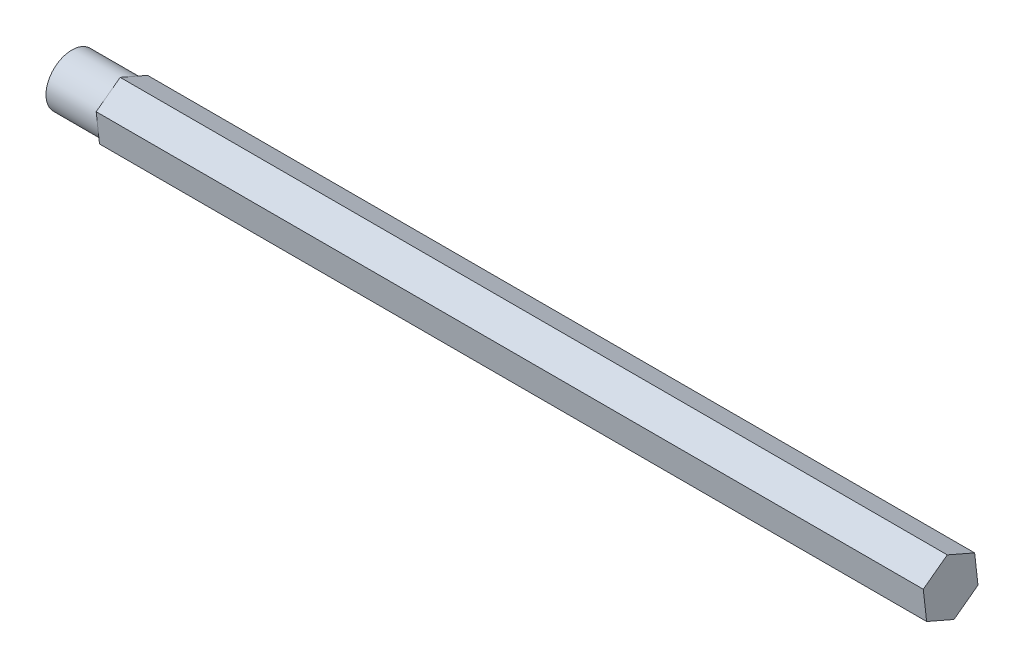
SolidWorks part; units mm, degrees
ref_plane "Front Plane" through (0, 0, 0) normal (0, 0, 1) x (1, 0, 0)
ref_plane "Top Plane" through (0, 0, 0) normal (0, 1, 0) x (1, 0, 0)
ref_plane "Right Plane" through (0, 0, 0) normal (1, 0, 0) x (0, 0, -1)
sketch "Sketch1" plane through (0, 0, 0) normal (1, 0, 0) x (0, 0, -1)
  line L1 (6.7219, -2.9291) -> (5.8976, 4.3568)
  line L2 (5.8976, 4.3568) -> (-0.8243, 7.2859)
  line L3 (-0.8243, 7.2859) -> (-6.7219, 2.9291)
  line L4 (-6.7219, 2.9291) -> (-5.8976, -4.3568)
  line L5 (-5.8976, -4.3568) -> (0.8243, -7.2859)
  line L6 (0.8243, -7.2859) -> (6.7219, -2.9291)
  circle A0 centre (0, 0) radius 6.35 construction
extrude "Boss-Extrude1" add sketch "Sketch1" along normal blind 203.2
sketch "Sketch2" plane through (0, 0, 0) normal (-1, 0, 0) x (0, 0, 1)
  circle A0 centre (0, 0) radius 6.35
extrude "Boss-Extrude2" add sketch "Sketch2" along normal blind 12.7
